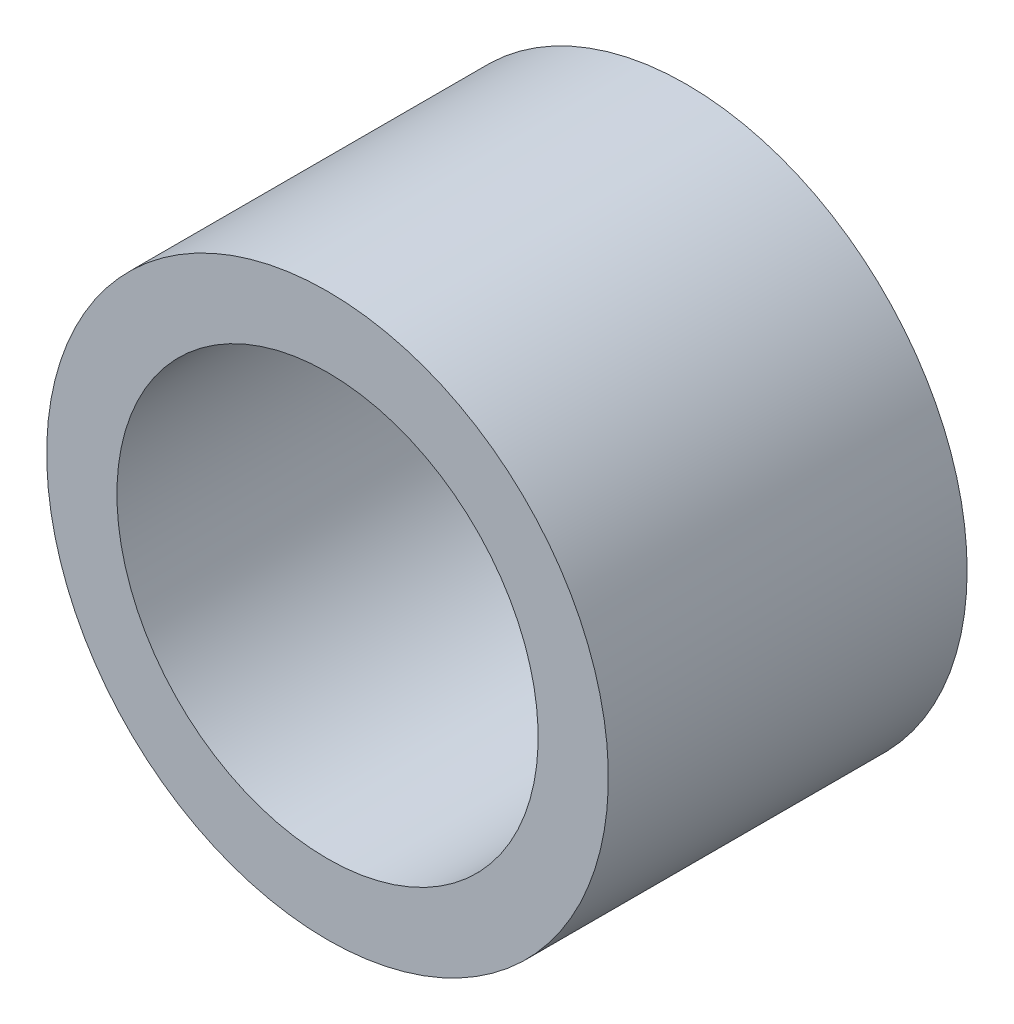
SolidWorks part; units mm, degrees
material "6061-T6 (SS)"
ref_plane "Front Plane" through (0, 0, 0) normal (0, 0, 1) x (1, 0, 0)
ref_plane "Top Plane" through (0, 0, 0) normal (0, 1, 0) x (1, 0, 0)
ref_plane "Right Plane" through (0, 0, 0) normal (1, 0, 0) x (0, 0, -1)
sketch "Sketch1" plane through (0, 0, 0) normal (0, 0, 1) x (1, 0, 0)
  circle A0 centre (0, 0) radius 12.7
  circle A2 centre (0, 0) radius 9.525
  dimension "D1" = 19.05
  dimension "D2" = 25.4
extrude "Boss-Extrude1" add sketch "Sketch1" along normal up to surface (16.2243 mm away)
equation "\"Thick\"= \"in\""
